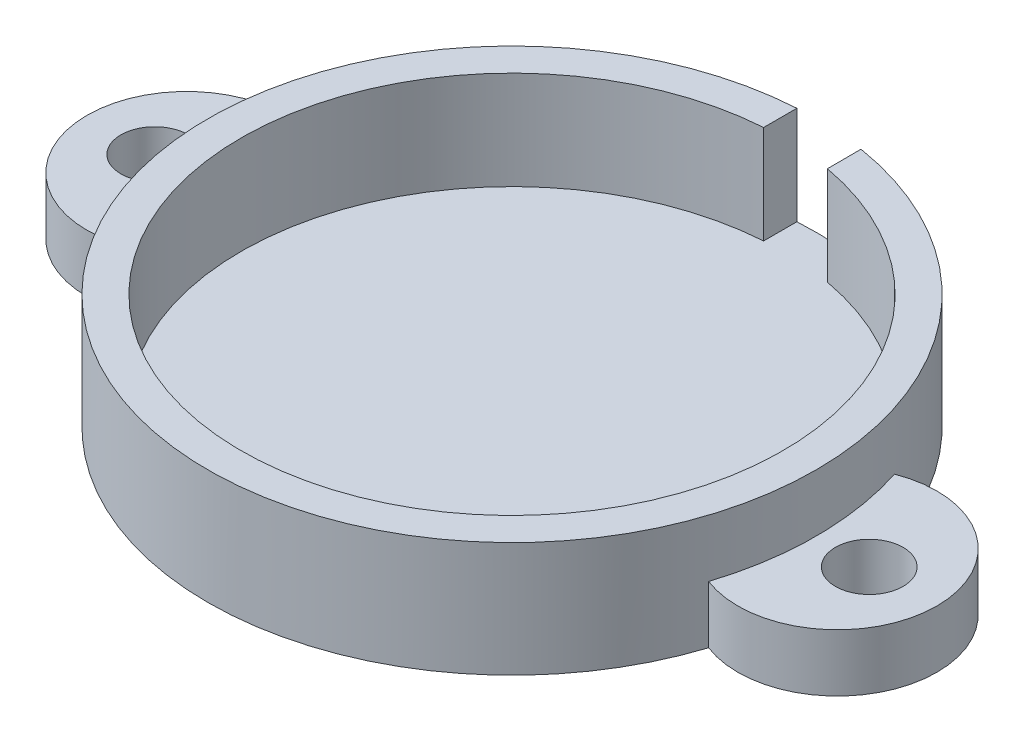
SolidWorks part; units mm, degrees
ref_plane "Front Plane" through (0, 0, 0) normal (0, 0, 1) x (1, 0, 0)
ref_plane "Top Plane" through (0, 0, 0) normal (0, 1, 0) x (1, 0, 0)
ref_plane "Right Plane" through (0, 0, 0) normal (1, 0, 0) x (0, 0, -1)
sketch "Sketch1" plane through (0, 0, 0) normal (0, 1, 0) x (1, 0, 0)
  circle A0 centre (0, 0) radius 58.166
  dimension "D1" = 116.332
extrude "Boss-Extrude1" add sketch "Sketch1" along normal blind 21.971 contours A0
sketch "Sketch3" plane through (0, 21.971, 0) normal (0, 1, 0) x (1, 0, 0)
  circle A0 centre (0, 0) radius 51.816
  dimension "D1" = 103.632
extrude "Cut-Extrude2" cut sketch "Sketch3" against normal blind 18.796
sketch "Sketch6" plane through (0, 21.971, 0) normal (0, 1, 0) x (1, 0, 0)
  line L0 (9.363, 50.963) -> (9.3408, 57.4111)
  line L1 (-3.5704, 51.6928) -> (-3.5704, 58.0563)
  arc A0 (9.3408, 57.4111) -> (-3.5704, 58.0563) centre (0, 0) ccw
  circle A1 centre (0, 0) radius 58.166 construction
  circle A2 centre (0, 0) radius 58.166 construction
  arc A3 (9.363, 50.963) -> (-3.5704, 51.6928) centre (0, 0) ccw
  circle A4 centre (0, 0) radius 51.816 construction
  circle A5 centre (0, 0) radius 51.816 construction
  point P12 (0, 51.689)
  point P15 (0, 53.2765)
  point P16 (-3.5704, 51.6928)
  point P17 (-3.5704, 58.0563)
  dimension "D1" = 12.954
  dimension "D2" = 12.954
extrude "Cut-Extrude7" cut sketch "Sketch6" against normal blind 18.796
sketch "Sketch7" plane through (0, 0, 0) normal (0, -1, 0) x (1, 0, 0)
  circle A5 centre (0, 0) radius 58.166 construction
  arc A7 (55.3829, -17.7769) -> (55.3829, 17.7769) centre (62.23, 0) ccw
  arc A8 (-55.3829, 17.7769) -> (-55.3829, -17.7769) centre (-62.23, 0) ccw
  circle A11 centre (-68.3238, 0) radius 6.477
  arc A12 (-55.3829, -17.7769) -> (-55.3829, 17.7769) centre (0, 0) cw
  arc A13 (55.3829, 17.7769) -> (55.3829, -17.7769) centre (0, 0) cw
  circle A14 centre (68.326, 0) radius 6.477
  dimension "D2" = 62.23
  dimension "D3" = 62.23
  dimension "D4" = 38.1
  dimension "D5" = 12.954
  dimension "D6" = 12.954
  dimension "D7" = 68.3238
  dimension "D1" = 38.1
  dimension "D8" = 68.326
extrude "Boss-Extrude3" add sketch "Sketch7" against normal blind 10.9855
